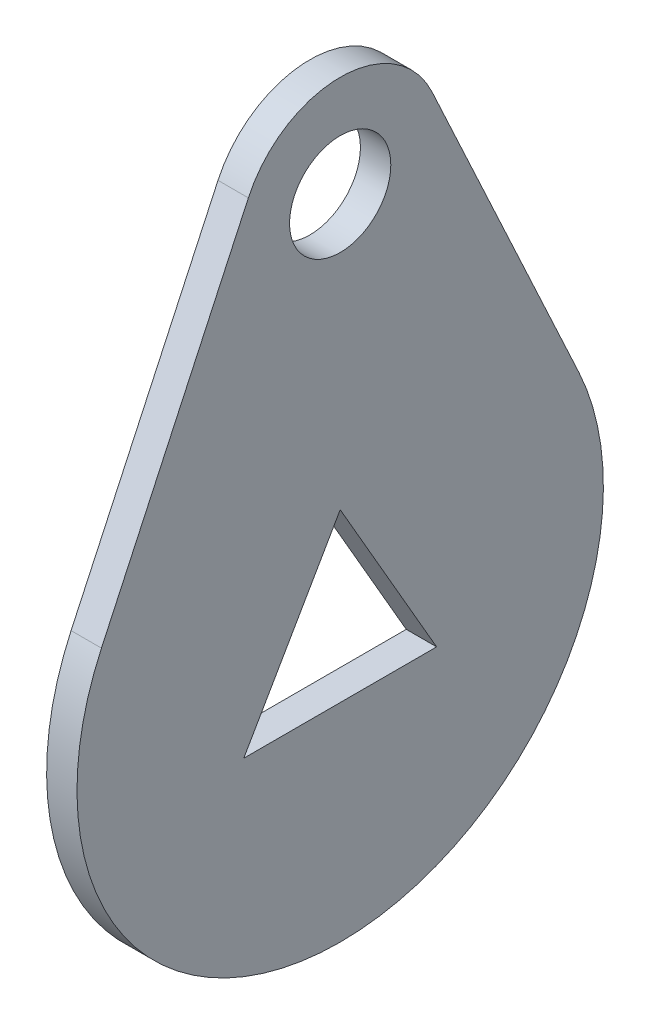
SolidWorks part; units mm, degrees
material "1023 Carbon Steel Sheet (SS)"
ref_plane "Płaszczyzna XY" through (0, 0, 0) normal (0, 0, 1) x (1, 0, 0)
ref_plane "Płaszczyzna XZ" through (0, 0, 0) normal (0, 1, 0) x (1, 0, 0)
ref_plane "Płaszczyzna YZ" through (0, 0, 0) normal (1, 0, 0) x (0, 0, -1)
sketch "Sketch1" plane through (0, 0, 0) normal (1, 0, 0) x (0, 0, -1)
  line L0 (0, 19) -> (0, 0)
  line L1 (-11.7915, 5.4737) -> (-4.5352, 21.1053)
  line L2 (4.5352, 21.1053) -> (11.7915, 5.4737)
  line L3 (4.7631, -2.75) -> (-4.7631, -2.75)
  line L4 (-4.7631, -2.75) -> (0, 5.5)
  line L5 (0, 5.5) -> (4.7631, -2.75)
  arc A0 (-11.7915, 5.4737) -> (11.7915, 5.4737) centre (0, 0) ccw
  arc A1 (4.5352, 21.1053) -> (-4.5352, 21.1053) centre (0, 19) ccw
  circle A2 centre (0, 19) radius 2.5
  dimension "D2" = 26
  dimension "D3" = 10
  dimension "D4" = 5
  dimension "D5" = 5.5
  dimension "D1" = 19
  dimension "D6" = 60
  dimension "D7" = 2.75
  dimension "D8" = 60
extrude "Boss-Extrude1" add sketch "Sketch1" along normal blind 1.5
